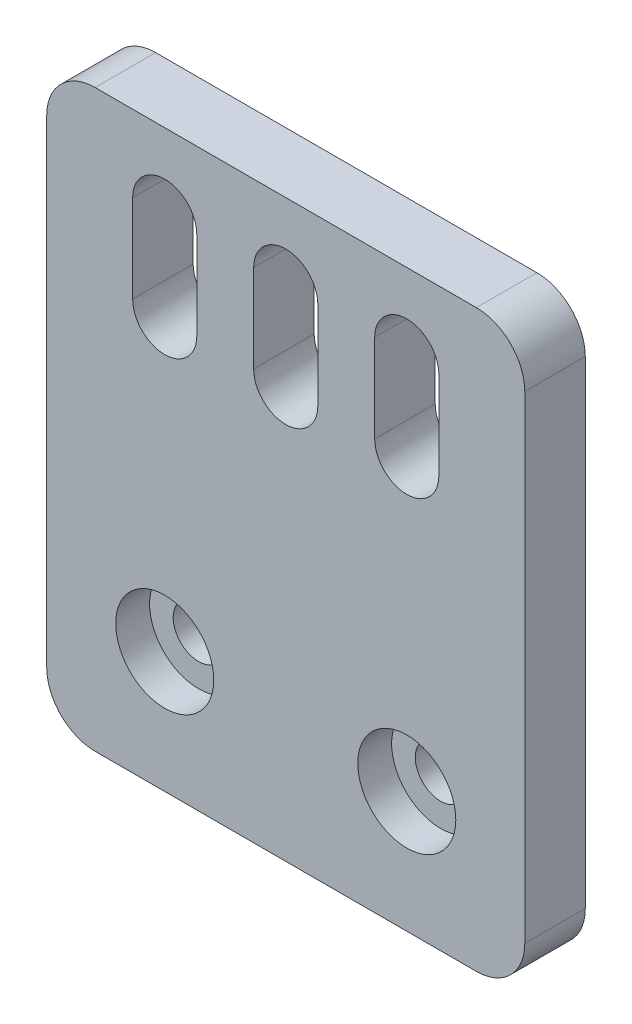
SolidWorks part; units mm, degrees
ref_plane "Alzado" through (0, 0, 0) normal (0, 0, 1) x (1, 0, 0)
ref_plane "Planta" through (0, 0, 0) normal (0, 1, 0) x (1, 0, 0)
ref_plane "Vista lateral" through (0, 0, 0) normal (1, 0, 0) x (0, 0, -1)
sketch "Croquis2" plane through (0, 0, 0) normal (0, 0, 1) x (1, 0, 0)
  line L0 (9.75, 41.1713) -> (9.75, 33.9113) construction
  line L1 (0, 47.5) -> (39.5, 47.5)
  line L2 (0, 47.5) -> (0, 0)
  line L3 (0, 0) -> (39.5, 0)
  line L4 (39.5, 47.5) -> (39.5, 0)
  line L5 (12.4, 41.1713) -> (12.4, 33.9113)
  line L6 (7.1, 41.1713) -> (7.1, 33.9113)
  line L7 (19.75, 41.1713) -> (19.75, 33.9113) construction
  line L8 (22.4, 41.1713) -> (22.4, 33.9113)
  line L9 (17.1, 41.1713) -> (17.1, 33.9113)
  line L10 (29.75, 41.1713) -> (29.75, 33.9113) construction
  line L11 (32.4, 41.1713) -> (32.4, 33.9113)
  line L12 (27.1, 41.1713) -> (27.1, 33.9113)
  line L23 (9.75, 10) -> (29.75, 10) construction
  line L24 (19.75, 10) -> (19.75, 0) construction
  circle A0 centre (9.75, 10) radius 2.1
  circle A1 centre (29.75, 10) radius 2.1
  arc A2 (12.4, 41.1713) -> (7.1, 41.1713) centre (9.75, 41.1713) ccw
  arc A3 (7.1, 33.9113) -> (12.4, 33.9113) centre (9.75, 33.9113) ccw
  arc A4 (22.4, 41.1713) -> (17.1, 41.1713) centre (19.75, 41.1713) ccw
  arc A5 (17.1, 33.9113) -> (22.4, 33.9113) centre (19.75, 33.9113) ccw
  arc A6 (32.4, 41.1713) -> (27.1, 41.1713) centre (29.75, 41.1713) ccw
  arc A7 (27.1, 33.9113) -> (32.4, 33.9113) centre (29.75, 33.9113) ccw
  point P10 (9.75, 37.5413)
  point P15 (19.75, 37.5413)
  point P22 (29.75, 37.5413)
  dimension "D3" = 4.2
  dimension "D11" = 2.65
  dimension "D12" = 10
  dimension "D1" = 47.5
  dimension "D2" = 39.5
  dimension "D4" = 27.5413
  dimension "D7" = 10
  dimension "D8" = 20
  dimension "D9" = 7.26
  dimension "D13" = 10
extrude "Saliente-Extruir1" add sketch "Croquis2" along normal blind 5
fillet "Redondeo1" radius 4 4 edges at (0, 0, 2.5) (39.5, 0, 2.5) (39.5, 47.5, 2.5) (0, 47.5, 2.5)
sketch "Croquis3" plane through (0, 0, 5) normal (0, 0, 1) x (1, 0, 0)
  circle A0 centre (29.75, 10) radius 4.05
  circle A1 centre (9.75, 10) radius 4.05
  dimension "D1" = 8.1
extrude "Cortar-Extruir1" cut sketch "Croquis3" against normal blind 2.8
